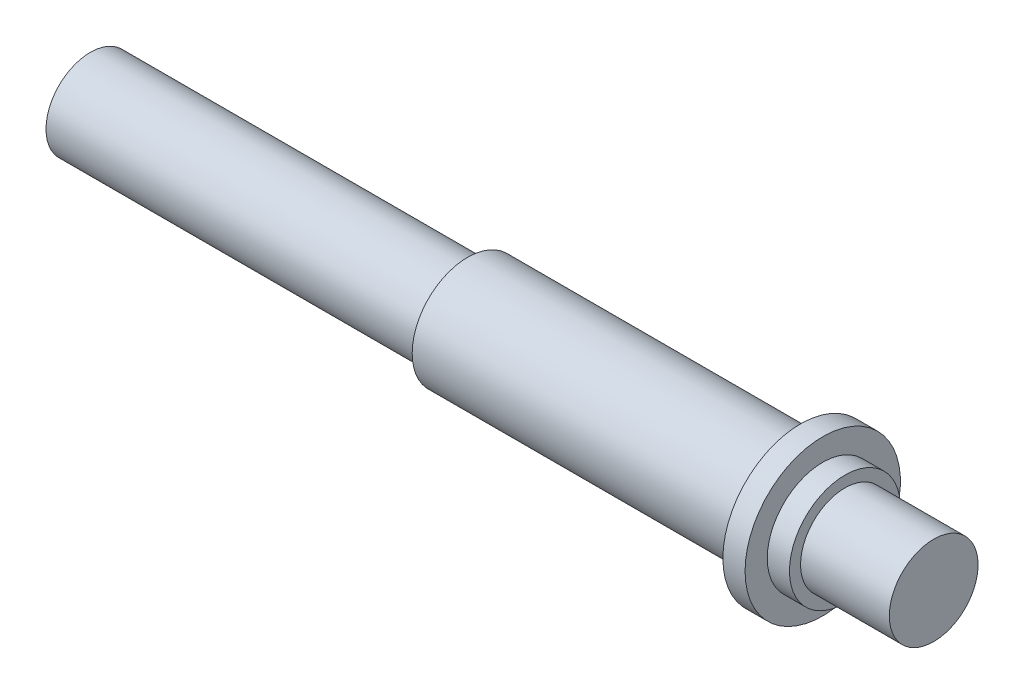
SolidWorks part; units mm, degrees
material "普通碳钢"
ref_plane "前视基准面" through (0, 0, 0) normal (0, 0, 1) x (1, 0, 0)
ref_plane "上视基准面" through (0, 0, 0) normal (0, 1, 0) x (1, 0, 0)
ref_plane "右视基准面" through (0, 0, 0) normal (1, 0, 0) x (0, 0, -1)
sketch "草图1" plane through (0, 0, 0) normal (0, 0, 1) x (1, 0, 0)
  line L0 (-56.8445, 0) -> (51.6534, 0) construction
  line L1 (-54.837, 0) -> (-54.837, 2)
  line L2 (-54.837, 2) -> (-37.837, 2)
  line L3 (-37.837, 2) -> (-37.837, 2.5)
  line L4 (-37.837, 2.5) -> (-22.837, 2.5)
  line L5 (-22.837, 2.5) -> (-22.837, 3.5)
  line L6 (-22.837, 3.5) -> (-21.837, 3.5)
  line L7 (-21.837, 3.5) -> (-21.837, 2.5)
  line L8 (-21.837, 2.5) -> (-20.837, 2.5)
  line L9 (-20.837, 2.5) -> (-20.837, 2)
  line L10 (-20.837, 2) -> (-16.837, 2)
  line L11 (-16.837, 2) -> (-16.837, 0)
  line L12 (-54.837, 0) -> (-16.837, 0)
  dimension "D1" = 2
  dimension "D2" = 17
  dimension "D3" = 15
  dimension "D4" = 1
  dimension "D5" = 1
  dimension "D6" = 5
  dimension "D7" = 7
  dimension "D8" = 2.5
  dimension "D9" = 4
  dimension "D10" = 2
revolve "旋转1" add sketch "草图1" angle 360 about L0
